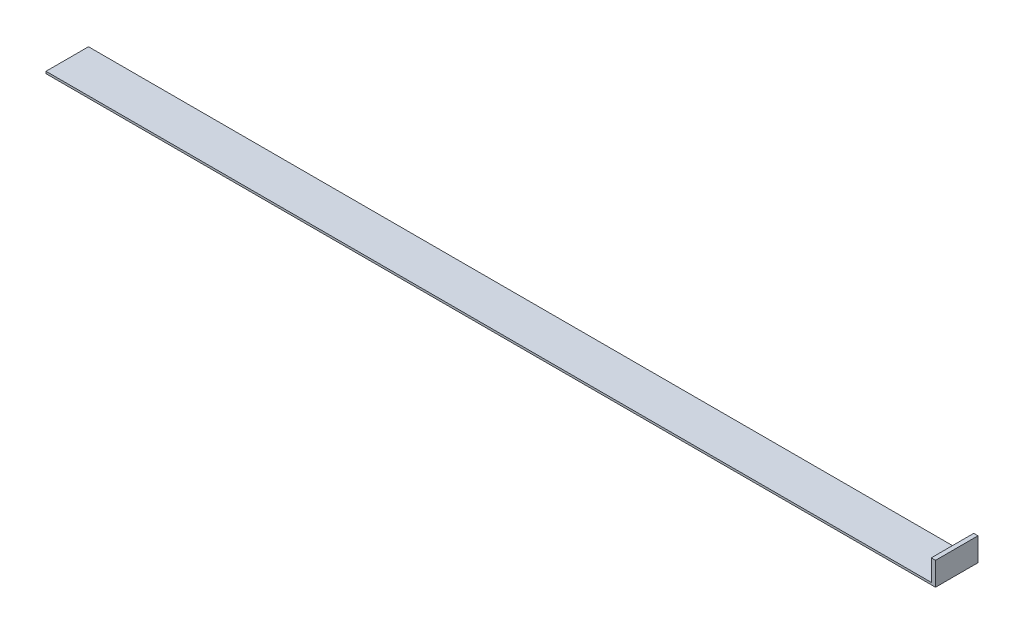
SolidWorks part; units mm, degrees
ref_plane "Front Plane" through (0, 0, 0) normal (0, 0, 1) x (1, 0, 0)
ref_plane "Top Plane" through (0, 0, 0) normal (0, 1, 0) x (1, 0, 0)
ref_plane "Right Plane" through (0, 0, 0) normal (1, 0, 0) x (0, 0, -1)
sketch "Sketch1" plane through (0, 0, 0) normal (0, 1, 0) x (1, 0, 0)
  line L1 (0, 0) -> (209.39, 0)
  line L2 (0, 0) -> (0, 10)
  line L3 (0, 10) -> (209.39, 10)
  line L4 (209.39, 0) -> (209.39, 10)
  dimension "D1" = 209.39
  dimension "D2" = 10
extrude "Boss-Extrude1" add sketch "Sketch1" along normal blind 0.5
sketch "Sketch2" plane through (0, 0.5, 0) normal (0, 1, 0) x (1, 0, 0)
  line L0 (0, 0) -> (209.39, 0) construction
  line L1 (209.39, 10) -> (208.39, 10)
  line L2 (209.39, 10) -> (209.39, 0)
  line L3 (209.39, 0) -> (208.39, 0)
  line L4 (208.39, 10) -> (208.39, 0)
  dimension "D1" = 1
extrude "Boss-Extrude2" add sketch "Sketch2" along normal blind 5
